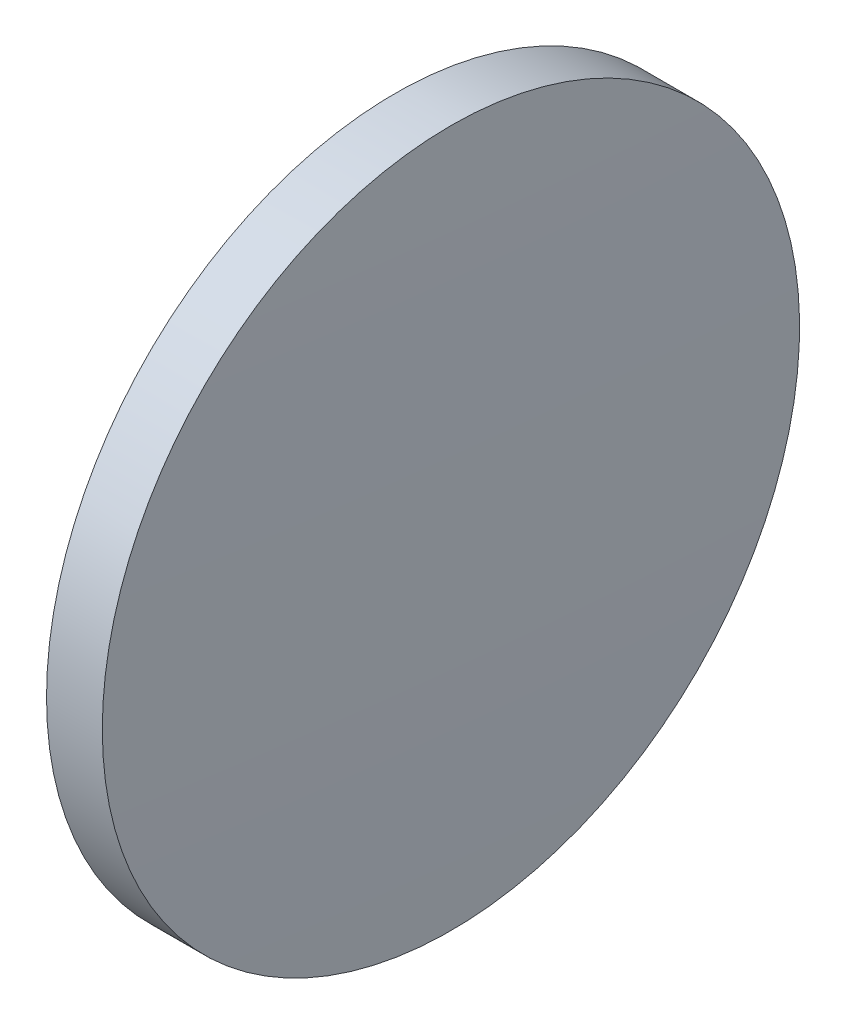
SolidWorks part; units mm, degrees
ref_plane "前视基准面" through (0, 0, 0) normal (0, 0, 1) x (1, 0, 0)
ref_plane "上视基准面" through (0, 0, 0) normal (0, 1, 0) x (1, 0, 0)
ref_plane "右视基准面" through (0, 0, 0) normal (1, 0, 0) x (0, 0, -1)
sketch "草图1" plane through (0, 0, 0) normal (0, 0, 1) x (1, 0, 0)
  line L0 (421.8357, 122.3871) -> (435.2814, 122.3871) construction
  line L1 (426.5777, 122.3871) -> (426.5777, 134.8871)
  line L2 (428.7277, 122.3871) -> (426.5777, 122.3871)
  line L5 (426.5777, 134.8871) -> (428.5777, 134.8871)
  arc A0 (428.7277, 122.3871) -> (428.5777, 134.8871) centre (-92.1806, 122.3871) ccw
revolve "旋转1" add sketch "草图1" angle 360 about L0
